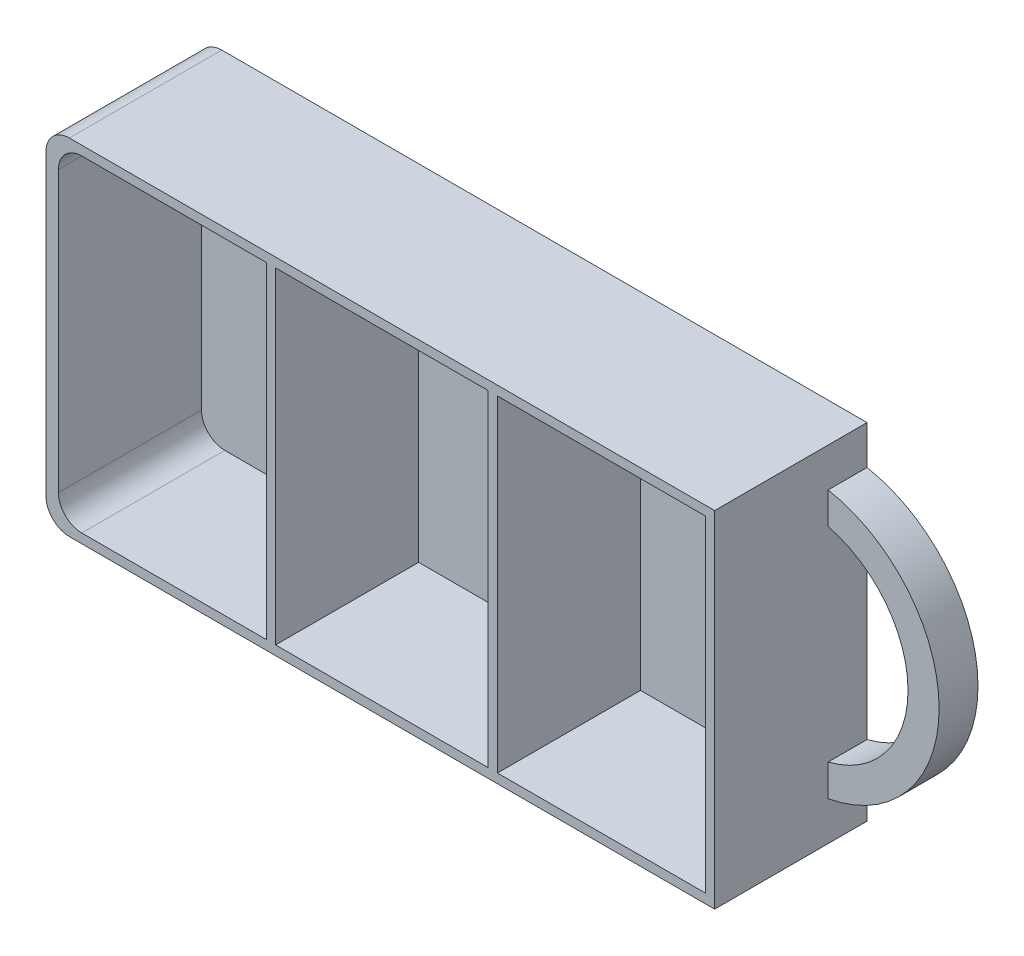
SolidWorks part; units mm, degrees
ref_plane "Спереди" through (0, 0, 0) normal (0, 0, 1) x (1, 0, 0)
ref_plane "Сверху" through (0, 0, 0) normal (0, 1, 0) x (1, 0, 0)
ref_plane "Справа" through (0, 0, 0) normal (1, 0, 0) x (0, 0, -1)
other "Configuration Table"
sketch "Эскиз1" plane through (0, 0, 0) normal (0, 0, 1) x (1, 0, 0)
  line L1 (-43, 22.2) -> (43, 22.2)
  line L2 (-43, 22.2) -> (-43, -22.2)
  line L3 (-43, -22.2) -> (43, -22.2)
  line L4 (43, 22.2) -> (43, -22.2)
  line L5 (-43, 22.2) -> (43, -22.2) construction
  line L6 (-43, -22.2) -> (43, 22.2) construction
  point P0 (0, 0)
  dimension "D1" = 86
  dimension "D2" = 44.4
extrude "Бобышка-Вытянуть1" add sketch "Эскиз1" along normal blind 19.6
sketch "Эскиз2" plane through (0, 0, 0) normal (0, 0, 1) x (1, 0, 0)
  line L0 (0, 0) -> (43, 0) construction
  line L1 (43, -22.2) -> (43, 22.2) construction
  line L2 (43, 17.2) -> (43, 13.1088)
  line L3 (43, -17.2) -> (43, -13.1088)
  arc A0 (43, -17.2) -> (43, 17.2) centre (39.7735, 0) ccw
  arc A1 (43, -13.1088) -> (43, 13.1088) centre (39.7735, 0) ccw
  dimension "D3" = 13.5
  dimension "D4" = 4
  dimension "D1" = 5
  dimension "D2" = 5
extrude "Бобышка-Вытянуть2" add sketch "Эскиз2" along normal blind 5
sketch "Эскиз3" plane through (0, 0, 19.6) normal (0, 0, 1) x (1, 0, 0)
  line L0 (41.8, 0) -> (-41.4, 0) construction
  line L2 (-14.6667, -21) -> (-13.4667, -21)
  line L3 (-14.6667, -21) -> (-14.6667, 21)
  line L4 (-14.6667, 21) -> (-13.4667, 21)
  line L5 (-41.4, 22.2) -> (-41.4, -22.2)
  line L6 (-43, -21) -> (41.8, -21)
  line L7 (41.8, -21) -> (41.8, 21)
  line L8 (41.8, 21) -> (-43, 21)
  line L9 (-41.4, -21) -> (41.8, -21)
  line L10 (41.8, -21) -> (41.8, 21)
  line L11 (41.8, 21) -> (-41.4, 21)
  line L12 (-41.4, 21) -> (-41.4, -21)
  line L13 (-13.4667, -21) -> (-13.4667, 21)
  line L14 (-14.6667, -21) -> (-13.4667, 21) construction
  line L15 (-14.6667, 21) -> (-13.4667, -21) construction
  line L16 (13.8667, 21) -> (15.0667, 21)
  line L17 (13.8667, 21) -> (13.8667, -21)
  line L18 (13.8667, -21) -> (15.0667, -21)
  line L19 (15.0667, 21) -> (15.0667, -21)
  line L20 (13.8667, 21) -> (15.0667, -21) construction
  line L21 (13.8667, -21) -> (15.0667, 21) construction
  point P9 (-14.0667, 0)
  point P15 (14.4667, 0)
  dimension "D3" = 1.2
  dimension "D4" = 1.2
  dimension "D5" = 83.2
  dimension "D6" = 27.3333
  dimension "D7" = 27.3333
  dimension "D8" = 27.3333
  dimension "D1" = 1.2
  dimension "D2" = 1.6
extrude "Вырез-Вытянуть1" cut sketch "Эскиз3" against normal offset from surface (18.4 mm away) 1.2 contours L11 L12 L9 L3 | L17 L11 L13 L9 | L11 L19 L9 L10 up to face at (48.1368, 0, 0)
fillet "Скругление1" radius 3 4 edges at (-43, 22.2, 9.8) (-43, -22.2, 9.8) (-41.4, -21, 10.4) (-41.4, 21, 10.4)
equation "\"D4@Эскиз3\"=\"D3@Эскиз3\""
equation "\"D6@Эскиз3\"=(\"D5@Эскиз3\"/3)-0.4"
equation "\"D7@Эскиз3\"=(\"D5@Эскиз3\"/3)-0.4"
